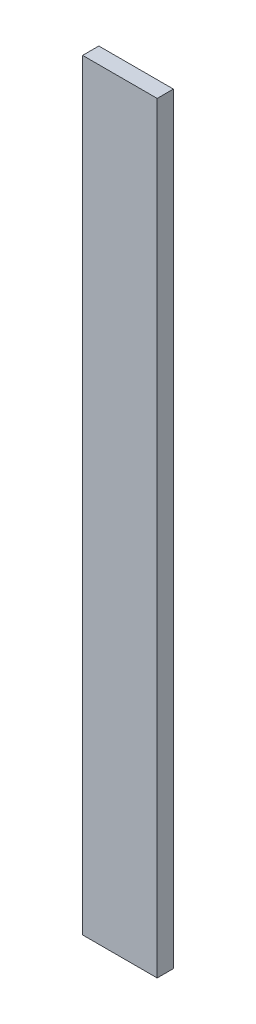
SolidWorks part; units mm, degrees
ref_plane "Front Plane" through (0, 0, 0) normal (0, 0, 1) x (1, 0, 0)
ref_plane "Top Plane" through (0, 0, 0) normal (0, 1, 0) x (1, 0, 0)
ref_plane "Right Plane" through (0, 0, 0) normal (1, 0, 0) x (0, 0, -1)
sketch "Sketch1" plane through (0, 0, 0) normal (0, 0, 1) x (1, 0, 0)
  line L1 (-1.15, -11.75) -> (1.15, -11.75)
  line L2 (-1.15, -11.75) -> (-1.15, 11.75)
  line L3 (-1.15, 11.75) -> (1.15, 11.75)
  line L4 (1.15, -11.75) -> (1.15, 11.75)
  line L5 (-1.15, -11.75) -> (1.15, 11.75) construction
  line L6 (-1.15, 11.75) -> (1.15, -11.75) construction
  point P0 (0, 0)
  dimension "D1" = 2.3
  dimension "D2" = 23.5
extrude "Boss-Extrude1" add sketch "Sketch1" against normal blind 0.5
